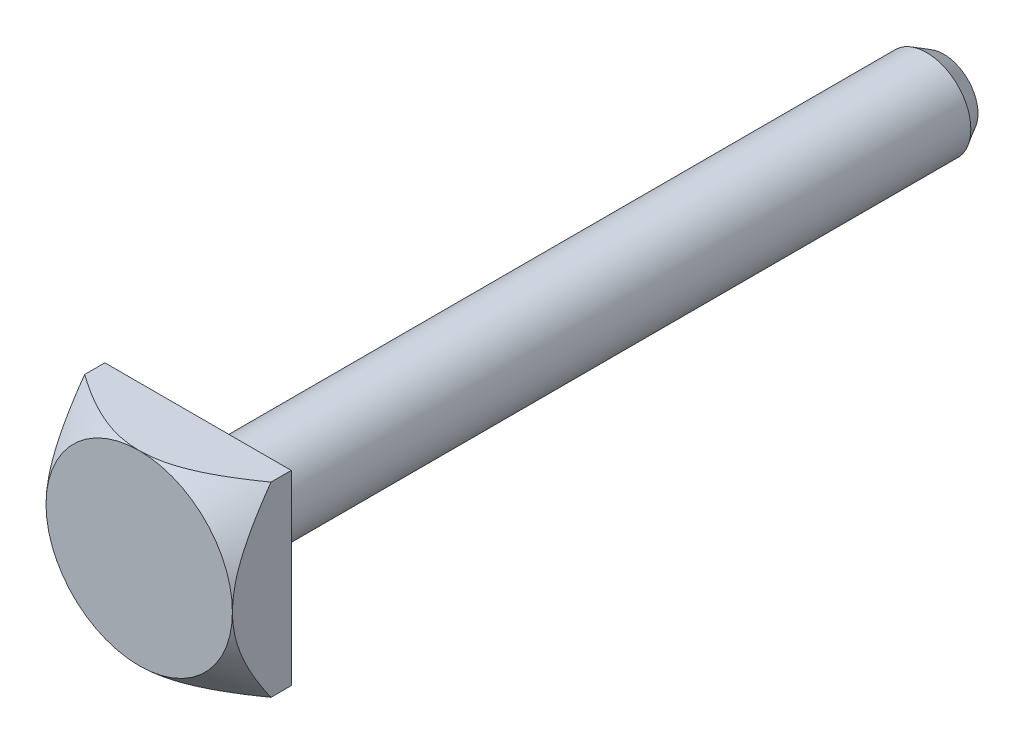
SolidWorks part; units mm, degrees
ref_plane "Front Plane" through (0, 0, 0) normal (0, 0, 1) x (1, 0, 0)
ref_plane "Top Plane" through (0, 0, 0) normal (0, 1, 0) x (1, 0, 0)
ref_plane "Right Plane" through (0, 0, 0) normal (1, 0, 0) x (0, 0, -1)
sketch "Sketch2" plane through (0, 0, 0) normal (0, 0, 1) x (1, 0, 0)
  circle A0 centre (0, 0) radius 4.5
extrude "Boss-Extrude1" add sketch "Sketch2" along normal blind 76
sketch "Sketch3" plane through (0, 0, 76) normal (0, 0, 1) x (1, 0, 0)
  line L1 (-9.5, 9.5) -> (9.5, 9.5)
  line L2 (-9.5, 9.5) -> (-9.5, -9.5)
  line L3 (-9.5, -9.5) -> (9.5, -9.5)
  line L4 (9.5, 9.5) -> (9.5, -9.5)
  line L5 (-9.5, 9.5) -> (9.5, -9.5) construction
  line L6 (-9.5, -9.5) -> (9.5, 9.5) construction
  point P0 (0, 0)
  dimension "D1" = 19
  dimension "D2" = 19
extrude "Boss-Extrude2" add sketch "Sketch3" along normal blind 6
chamfer "Chamfer1" distance 1 angle 60 1 edges at (4.5, 0, 0)
sketch "Sketch4" plane through (0, 0, 82) normal (0, 0, 1) x (1, 0, 0)
  circle A0 centre (0, 0) radius 9.5
extrude "Cut-Extrude1" cut sketch "Sketch4" against normal blind 6 draft 45 flip side to cut
